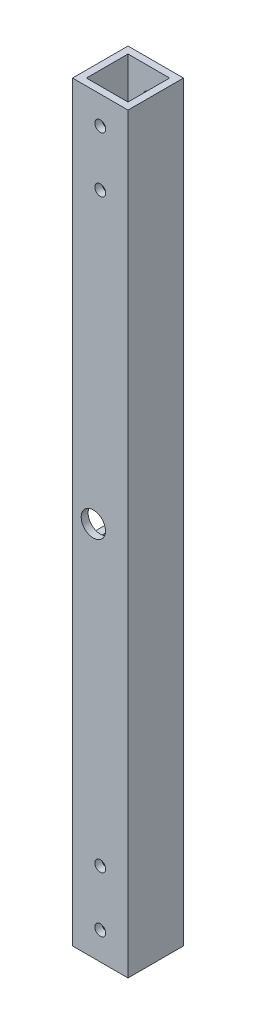
SolidWorks part; units mm, degrees
material "6061-T6 (SS)"
ref_plane "Front Plane" through (0, 0, 0) normal (0, 0, 1) x (1, 0, 0)
ref_plane "Top Plane" through (0, 0, 0) normal (0, 1, 0) x (1, 0, 0)
ref_plane "Right Plane" through (0, 0, 0) normal (1, 0, 0) x (0, 0, -1)
sketch "Sketch1" plane through (0, 0, 0) normal (0, 1, 0) x (1, 0, 0)
  line L0 (0, 12.7) -> (0, -12.7)
  line L1 (0, -12.7) -> (25.4, -12.7)
  line L3 (22.225, -9.525) -> (3.175, -9.525)
  line L4 (3.175, -9.525) -> (3.175, 9.525)
  line L5 (3.175, 9.525) -> (22.225, 9.525)
  line L7 (25.4, 12.7) -> (0, 12.7)
  line L8 (0, 0) -> (3.175, 0) construction
  line L9 (25.4, 12.7) -> (25.4, -12.7)
  line L10 (22.225, 9.525) -> (22.225, -9.525)
  line L11 (12.7, 12.7) -> (12.7, 9.525) construction
  line L12 (12.7, -12.7) -> (12.7, -9.525) construction
  point P5 (0, 0)
  dimension "D1" = 25.4
  dimension "D2" = 3.175
  dimension "D3" = 25.4
extrude "Boss-Extrude1" add sketch "Sketch1" along normal mid plane 344.17
sketch "Sketch2" plane through (0, 0, 0) normal (-1, 0, 0) x (0, 0, 1)
  line L1 (-9.525, -12.7) -> (9.525, -12.7)
  line L2 (-9.525, -12.7) -> (-9.525, 12.7)
  line L3 (-9.525, 12.7) -> (9.525, 12.7)
  line L4 (9.525, -12.7) -> (9.525, 12.7)
  line L5 (-9.525, -12.7) -> (9.525, 12.7) construction
  line L6 (-9.525, 12.7) -> (9.525, -12.7) construction
  point P0 (0, 0)
  dimension "D1" = 25.4
  dimension "D2" = 19.05
extrude "Cut-Extrude1" cut sketch "Sketch2" against normal up to surface (3.175 mm away) up to face at (3.175, 0, 0)
sketch "Sketch3" plane through (0, 0, -12.7) normal (0, 0, -1) x (-1, 0, 0)
  line L0 (-12.7, -172.085) -> (-12.7, 172.085) construction
  line L1 (-25.4, -172.085) -> (0, -172.085) construction
  line L2 (-25.4, 172.085) -> (0, 172.085) construction
  line L3 (0, 172.085) -> (0, -172.085) construction
  line L4 (-9.525, 0) -> (-12.7, 0) construction
  circle A0 centre (-12.7, -159.385) radius 2.4892
  circle A1 centre (-12.7, -133.985) radius 2.4892
  circle A3 centre (-9.525, 0) radius 5.5562
  dimension "D1" = 25.4
  dimension "D2" = 12.7
  dimension "D3" = 4.9784
  dimension "D4" = 11.1125
  dimension "D5" = 9.525
extrude "Cut-Extrude2" cut sketch "Sketch3" against normal through all
mirror "Mirror1" about plane through (0, 0, 0) normal (0, 1, 0) of "Cut-Extrude2"
fillet "Fillet1" radius 6.35 4 edges at (1.5875, 12.7, 9.525) (1.5875, 12.7, -9.525) (1.5875, -12.7, -9.525) (1.5875, -12.7, 9.525)
equation "\"Thick\"= \"in\""
